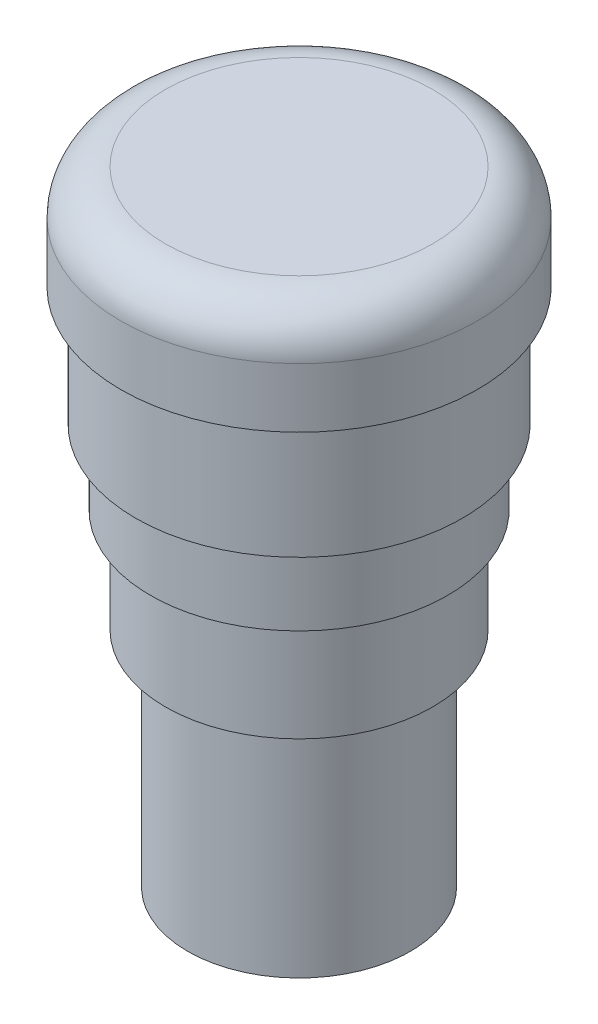
SolidWorks part; units mm, degrees
ref_plane "Face" through (0, 0, 0) normal (0, 0, 1) x (1, 0, 0)
ref_plane "Dessus" through (0, 0, 0) normal (0, 1, 0) x (1, 0, 0)
ref_plane "Droite" through (0, 0, 0) normal (1, 0, 0) x (0, 0, -1)
sketch "Esquisse1" plane through (0, 0, 0) normal (0, 1, 0) x (1, 0, 0)
  circle A0 centre (0, 0) radius 12
  dimension "D1" = 24
extrude "Extrusion1" add sketch "Esquisse1" along normal blind 7
sketch "Esquisse2" plane through (0, 0, 0) normal (0, -1, 0) x (1, 0, 0)
  circle A0 centre (0, 0) radius 11
  dimension "D1" = 22
extrude "Extrusion2" add sketch "Esquisse2" along normal blind 8
fillet "Congé1" radius 3 1 edges at (0, 7, 12)
sketch "Esquisse3" plane through (0, -8, 0) normal (0, -1, 0) x (1, 0, 0)
  circle A0 centre (0, 0) radius 10
  dimension "D1" = 20
extrude "Extrusion3" add sketch "Esquisse3" along normal blind 5
sketch "Esquisse4" plane through (0, -13, 0) normal (0, -1, 0) x (1, 0, 0)
  circle A0 centre (0, 0) radius 9
  dimension "D1" = 18
extrude "Extrusion4" add sketch "Esquisse4" along normal blind 7
sketch "Esquisse5" plane through (0, -20, 0) normal (0, -1, 0) x (1, 0, 0)
  circle A0 centre (0, 0) radius 7.5
  dimension "D1" = 15
extrude "Extrusion5" add sketch "Esquisse5" along normal blind 15
